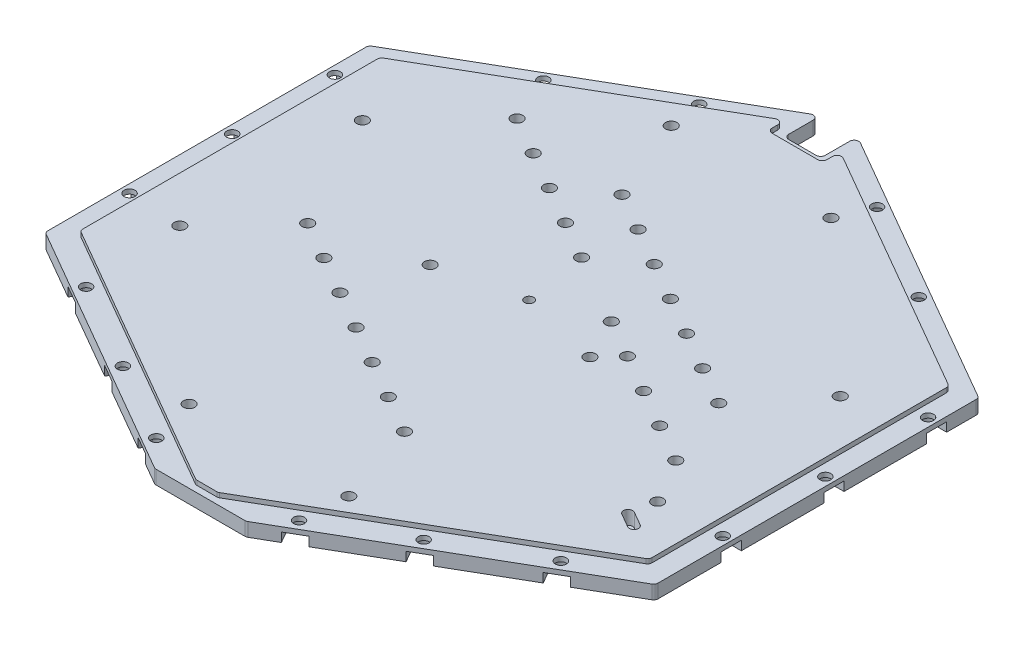
SolidWorks part; units mm, degrees
material "Copper"
ref_plane "Front Plane" through (0, 0, 0) normal (0, 0, 1) x (1, 0, 0)
ref_plane "Top Plane" through (0, 0, 0) normal (0, 1, 0) x (1, 0, 0)
ref_plane "Right Plane" through (0, 0, 0) normal (1, 0, 0) x (0, 0, -1)
sketch "Sketch1" plane through (0, 0, 0) normal (0, 1, 0) x (1, 0, 0)
  line L1 (-67.3538, -38.8868) -> (0, -77.7735)
  line L2 (0, -77.7735) -> (67.3538, -38.8868)
  line L3 (67.3538, -38.8868) -> (67.3538, 38.8868)
  line L4 (67.3538, 38.8868) -> (0, 77.7735)
  line L5 (0, 77.7735) -> (-67.3538, 38.8868)
  line L6 (-67.3538, 38.8868) -> (-67.3538, -38.8868)
  line L7 (-62.3538, -36) -> (0, -72) construction
  line L8 (0, -72) -> (62.3538, -36) construction
  line L9 (62.3538, -36) -> (62.3538, 36) construction
  line L10 (62.3538, 36) -> (0, 72) construction
  line L11 (0, 72) -> (-62.3538, 36) construction
  line L12 (-62.3538, 36) -> (-62.3538, -36) construction
  circle A0 centre (0, 0) radius 67.3538 construction
  circle A1 centre (0, 0) radius 62.3538 construction
  dimension "D1" = 5
  dimension "D2" = 72
extrude "Boss-Extrude1" add sketch "Sketch1" along normal blind 4
sketch "Sketch2" plane through (0, 4, 0) normal (0, 1, 0) x (1, 0, 0)
  line L0 (-67.3538, 38.8868) -> (-67.3538, 31.9585)
  line L1 (-67.3538, 38.8868) -> (-67.3538, -38.8868) construction
  line L2 (-67.3538, 31.9585) -> (0, 70.8453)
  line L3 (0, 70.8453) -> (67.3538, 31.9585)
  line L4 (67.3538, -38.8868) -> (67.3538, 38.8868) construction
  line L5 (67.3538, 31.9585) -> (67.3538, 38.8868)
  line L6 (67.3538, 38.8868) -> (0, 77.7735)
  line L7 (0, 77.7735) -> (-67.3538, 38.8868)
  line L8 (0, 77.7735) -> (-67.3538, 38.8868) construction
  dimension "D1" = 6
extrude "Cut-Extrude1" cut sketch "Sketch2" against normal up to next
sketch "Sketch4" plane through (0, 4, 0) normal (0, 1, 0) x (1, 0, 0)
  line L0 (-67.3538, 31.9585) -> (-67.3538, -38.8868)
  line L1 (-67.3538, 31.9585) -> (-67.3538, -38.8868) construction
  line L2 (-67.3538, -38.8868) -> (0, -77.7735)
  line L3 (0, -77.7735) -> (67.3538, -38.8868)
  line L4 (67.3538, -38.8868) -> (67.3538, 31.9585)
  line L7 (62.3538, 29.6491) -> (62.3538, -36)
  line L8 (62.3538, -36) -> (0, -72)
  line L9 (0, -72) -> (-62.3538, -36)
  line L10 (-62.3538, -36) -> (-62.3538, 29.6491)
  line L30 (-67.3538, 31.9585) -> (0, 70.8453)
  line L39 (0, 70.8453) -> (67.3538, 31.9585)
  line L40 (-62.3538, 29.6491) -> (0, 65.6491)
  line L41 (0, 65.6491) -> (62.3538, 29.6491)
  dimension "D1" = 5
  dimension "D2" = 5
  dimension "D3" = 5
  dimension "D4" = 4.5
extrude "Cut-Extrude3" cut sketch "Sketch4" against normal blind 1
sketch "Sketch5" plane through (0, 0, 0) normal (0, -1, 0) x (1, 0, 0)
  line L0 (0, 77.7735) -> (10, 72)
  line L1 (0, 77.7735) -> (67.3538, 38.8868) construction
  line L2 (10, 72) -> (-10, 72)
  line L3 (-67.3538, 38.8868) -> (0, 77.7735) construction
  line L4 (-10, 72) -> (0, 77.7735)
  line L5 (-4, -68.5359) -> (-4, -59.8859)
  line L6 (0, -70.8453) -> (0, -59.8859) construction
  line L7 (-4, -59.8859) -> (4, -59.8859)
  line L8 (4, -59.8859) -> (4, -68.5359)
  line L10 (4, -68.5359) -> (0, -70.8453)
  line L11 (0, -70.8453) -> (-4, -68.5359)
  line L15 (0, -70.8453) -> (-67.3538, -31.9585) construction
  line L16 (67.3538, -31.9585) -> (0, -70.8453) construction
  point P5 (0, 72)
  dimension "D1" = 8.65
  dimension "D2" = 8
extrude "Cut-Extrude4" cut sketch "Sketch5" against normal up to surface (3 mm away) up to face at (0, 3, 3.1754)
sketch "Sketch8" plane through (0, 4, 0) normal (0, 1, 0) x (1, 0, 0)
  line L0 (54.3431, -31.375) -> (51.312, -29.625) construction
  line L1 (53.8431, -32.241) -> (50.812, -30.491)
  line L2 (54.8431, -30.509) -> (51.812, -28.759)
  line L4 (-62.3538, 36) -> (62.3538, -36) construction
  line L7 (62.3538, 29.6491) -> (0, 65.6491) construction
  line L8 (0, 72) -> (0, -72) construction
  circle A0 centre (0, 0) radius 1
  arc A2 (53.8431, -32.241) -> (54.8431, -30.509) centre (54.3431, -31.375) ccw
  arc A3 (51.812, -28.759) -> (50.812, -30.491) centre (51.312, -29.625) ccw
  point P6 (52.8275, -30.5)
  dimension "D1" = 2
  dimension "D2" = 1
  dimension "D3" = 3.5
  dimension "D4" = 61
extrude "Cut-Extrude5" cut sketch "Sketch8" against normal offset from surface (3 mm away) 1 up to face at (0, 0, -9.8987)
sketch "Sketch16" plane through (0, 0, 0) normal (0, -1, 0) x (1, 0, 0)
  line L0 (67.3538, 38.8868) -> (66.8538, 39.1754)
  line L2 (-66.8538, -31.6699) -> (-66.8538, 39.1754)
  line L4 (67.3538, -31.9585) -> (67.3538, 38.8868)
  line L5 (67.3538, 38.8868) -> (67.3538, -38.8868) construction
  line L6 (0, 77.7735) -> (67.3538, 38.8868) construction
  line L7 (-67.3538, 38.8868) -> (-66.8538, 39.1754)
  line L9 (66.8538, -31.6699) -> (66.8538, 39.1754)
  line L11 (-67.3538, -31.9585) -> (-67.3538, 38.8868)
  line L12 (-67.3538, 38.8868) -> (0, 77.7735) construction
  line L13 (-67.3538, -38.8868) -> (-67.3538, 38.8868) construction
  line L15 (66.8538, -31.6699) -> (0, -70.2679)
  line L16 (0, -70.2679) -> (-66.8538, -31.6699)
  line L18 (-67.3538, -31.9585) -> (0, -70.8453)
  line L20 (0, -70.8453) -> (67.3538, -31.9585)
  line L22 (67.3538, -31.9585) -> (4, -68.5359) construction
  line L23 (-4, -68.5359) -> (-67.3538, -31.9585) construction
  line L24 (67.3538, 38.8868) -> (67.3538, -31.9585) construction
  dimension "D1" = 0.5
  dimension "D2" = 0.5
  dimension "D3" = 0.5
  dimension "D4" = 0.5
extrude "Cut-Extrude7" cut sketch "Sketch16" against normal through all
hole_wizard "Tap Drill for M3x0.5 Tap1" positions "Sketch9" profile "Sketch10" hole size "M3x0.5" standard "ANSI Metric" end condition through all
sketch "Sketch9" plane through (0, 4, 0) normal (0, 1, 0) x (1, 0, 0)
  line L0 (-5.9392, -68.571) -> (11.3328, -38.655) construction
  line L2 (-62.3538, -36) -> (0, -72) construction
  line L3 (-62.3538, -36) -> (0, -72) construction
  line L4 (-51.8644, 5.1642) -> (-35.7354, 33.1005) construction
  line L5 (-51.8644, 5.1642) -> (-18.4289, -14.1398) construction
  line L6 (-35.7354, 33.1005) -> (-2.2999, 13.7965) construction
  line L7 (-18.4289, -14.1398) -> (-2.2999, 13.7965) construction
  line L8 (-3.0309, -23.0298) -> (13.0981, 4.9065) construction
  line L9 (-3.0309, -23.0298) -> (30.4046, -42.3338) construction
  line L10 (13.0981, 4.9065) -> (46.5336, -14.3975) construction
  line L11 (30.4046, -42.3338) -> (46.5336, -14.3975) construction
  line L12 (-18.9587, 30.7468) -> (-16.9267, 34.2663) construction
  line L13 (-18.9587, 30.7468) -> (38.3216, -2.324) construction
  line L14 (-16.9267, 34.2663) -> (40.3536, 1.1956) construction
  line L15 (38.3216, -2.324) -> (40.3536, 1.1956) construction
  point P0 (11.3328, -38.655)
  point P1 (46.5336, -14.3975)
  point P3 (40.3536, 1.1956)
  point P411 (2.9739, -33.829)
  point P412 (-5.385, -29.003)
  point P413 (-13.7438, -24.177)
  point P414 (-22.1027, -19.351)
  point P415 (-30.4616, -14.525)
  point P416 (-38.8205, -9.699)
  point P431 (38.1747, -9.5715)
  point P432 (29.8158, -4.7455)
  point P433 (21.4569, 0.0805)
  point P434 (13.0981, 4.9065)
  point P437 (-2.2999, 13.7965)
  point P443 (-10.6588, 18.6225)
  point P444 (-19.0176, 23.4485)
  point P445 (-27.3765, 28.2745)
  point P446 (-35.7354, 33.1005)
  point P454 (31.9947, 6.0216)
  point P455 (23.6358, 10.8476)
  point P456 (15.2769, 15.6736)
  point P457 (6.9181, 20.4996)
  point P458 (-1.4408, 25.3256)
  point P459 (-9.7997, 30.1516)
  dimension "D1" = 34.544
  dimension "D2" = 6.858
  dimension "D3" = 7
  dimension "D4" = 32.258
  dimension "D5" = 4.064
  dimension "D6" = 32.258
  dimension "D7" = 6.35
  dimension "D8" = 6.35
  dimension "D11" = 4.826
  dimension "D12" = 7
  dimension "D13" = 8.89
  dimension "D14" = 8.89
  dimension "D9" = 5
  dimension "D10" = 5
sketch "Sketch10" plane through (11.3328, 4, 38.655) normal (1, 0, 0) x (0, 0, 1)
  line L0 (0, 0) -> (0, 4)
  line L1 (0, 4) -> (1.25, 4)
  line L2 (1.25, 4) -> (1.25, 0)
  line L5 (1.25, 0) -> (0, 0)
  line L11 (0, -6.35) -> (0, 107.95) construction
  dimension "Thru Hole Dia." = 2.5
  dimension "Thru Hole Depth" = 4
hole_wizard "Tap Drill for M3x0.5 Tap2" positions "Sketch11" profile "Sketch12" hole size "M3x0.5" standard "ANSI Metric" end condition through all
sketch "Sketch11" plane through (0, 0, 0) normal (0, -1, 0) x (-1, 0, 0)
  line L3 (17.5, -57) -> (-17.5, -57) construction
  line L4 (17.5, -57) -> (17.5, 48.637) construction
  line L5 (17.5, 48.637) -> (-17.5, 48.637) construction
  line L6 (-17.5, -57) -> (-17.5, 48.637) construction
  line L8 (52.3538, -24.1815) -> (-52.3538, -24.1815) construction
  line L9 (52.3538, -24.1815) -> (52.3538, 15.8185) construction
  line L10 (52.3538, 15.8185) -> (-52.3538, 15.8185) construction
  line L11 (-52.3538, -24.1815) -> (-52.3538, 15.8185) construction
  line L12 (-4, 59.8859) -> (4, 59.8859) construction
  line L15 (10, -72) -> (-10, -72) construction
  line L16 (0, -72) -> (0, 59.8859) construction
  line L17 (52.3538, -4.1815) -> (-52.3538, -4.1815) construction
  line L18 (-67.3538, -38.8868) -> (-67.3538, 38.8868) construction
  line L19 (67.3538, 38.8868) -> (67.3538, -38.8868) construction
  point P0 (-17.5, 48.637)
  point P2 (17.5, 48.637)
  point P8 (-52.3538, 15.8185)
  point P12 (-52.3538, -24.1815)
  point P20 (-17.5, -57)
  point P22 (17.5, -57)
  point P24 (52.3538, 15.8185)
  point P26 (52.3538, -24.1815)
  point P424 (0, 48.637)
  point P440 (17.5, -4.1815)
  point P441 (-17.5, -4.1815)
  dimension "D1" = 105.637
  dimension "D2" = 15
  dimension "D3" = 15
  dimension "D4" = 15
  dimension "D5" = 35
  dimension "D6" = 40
sketch "Sketch12" plane through (17.5, 0, -48.637) normal (1, 0, 0) x (0, 0, -1)
  line L0 (0, 0) -> (0, 4)
  line L1 (0, 4) -> (1.25, 4)
  line L2 (1.25, 4) -> (1.25, 0)
  line L5 (1.25, 0) -> (0, 0)
  line L11 (0, -6.35) -> (0, 107.95) construction
  dimension "Thru Hole Dia." = 2.5
  dimension "Thru Hole Depth" = 4
chamfer "Chamfer1" distance 2.8 1 edges at (0, 3.5, 72)
hole_wizard "CBORE for M2 SHCS2" positions "Sketch13" profile "Sketch14" counterbore size "M2" standard "ANSI Metric" end condition through all
sketch "Sketch13" plane through (0, 0, 79.328) normal (0, -1, 0) x (-1, 0, 0)
  point P0 (-65, 101.7487)
  point P1 (-41.1362, 123.5785)
  point P2 (-19.4856, 136.0785)
  point P3 (19.4856, 136.0785)
  point P4 (41.1362, 123.5785)
  point P5 (65, 101.7687)
  point P6 (65, 79.2687)
  point P7 (65, 56.7687)
  point P8 (52.0096, 34.2687)
  point P9 (32.9571, 23.2687)
  point P10 (15.6366, 13.2687)
  point P11 (-15.6366, 13.2687)
  point P12 (-32.9571, 23.2687)
  point P13 (-52.0096, 34.2687)
  point P14 (-65, 56.7487)
  point P15 (-65, 79.2487)
sketch "Sketch14" plane through (65, 0, -22.4207) normal (1, 0, 0) x (0, 0, -1)
  line L0 (0, 0) -> (0, 4)
  line L1 (0, 4) -> (1.2, 4)
  line L2 (1.2, 4) -> (1.2, 2)
  line L3 (1.2, 2) -> (2.2, 2)
  line L4 (2.2, 2) -> (2.2, 0)
  line L5 (2.2, 0) -> (0, 0)
  line L6 (0, -6.35) -> (0, 107.95) construction
  dimension "Thru Hole Dia." = 2.4
  dimension "Thru Hole Depth" = 4
  dimension "C'Bore Dia." = 4.4
  dimension "C'Bore Depth" = 2
sketch "Sketch15" plane through (0, 4, 0) normal (0, 1, 0) x (1, 0, 0)
  line L1 (6, 73.0491) -> (-6, 73.0491)
  line L2 (6, 73.0491) -> (6, 58.2491)
  line L3 (6, 58.2491) -> (-6, 58.2491)
  line L4 (-6, 73.0491) -> (-6, 58.2491)
  line L5 (6, 73.0491) -> (-6, 58.2491) construction
  line L6 (6, 58.2491) -> (-6, 73.0491) construction
  point P0 (0, 65.6491)
  dimension "D1" = 12
  dimension "D2" = 7.4
extrude "Cut-Extrude6" cut sketch "Sketch15" against normal up to surface (1 mm away) up to face at (65, 3, -23.6207)
fillet "Fillet1" radius 1 20 edges at (4, 1.5, -59.8859) (-4, 1.5, -59.8859) (62.3538, 3.5, -29.6491) (62.3538, 3.5, 36) (10, 1.5, 72) (-10, 1.5, 72) (-62.3538, 3.5, 36) (-62.3538, 3.5, -29.6491) (66.8538, 1.5, 39.1754) (66.8538, 1.5, -31.6699) (-66.8538, 1.5, 39.1754) (-66.8538, 1.5, -31.6699) (4, 1.5, -67.9585) (-4, 1.5, -67.9585) (6, 3.5, -58.2491) (-6, 3.5, -58.2491) (6, 3.5, -62.185) (-6, 3.5, -62.185) (-2.4249, 3.5, 70.6) (2.4249, 3.5, 70.6)
sketch "Sketch17" plane through (0, 0, 0) normal (0, -1, 0) x (1, 0, 0)
  line L0 (-65, 24.7593) -> (-66.8538, 24.7593)
  line L1 (21.3908, -55.6505) -> (22.3726, -57.3511)
  line L2 (-65, 20.3593) -> (-66.8538, 20.3593)
  line L3 (22.3726, -57.3511) -> (18.5621, -59.5511)
  line L4 (-66.8538, 20.3593) -> (-66.8538, 24.7593)
  line L5 (18.5621, -59.5511) -> (17.5803, -57.8505)
  line L6 (21.3908, -55.6505) -> (17.5803, -57.8505) construction
  line L7 (-65, 2.2593) -> (-66.8538, 2.2593)
  line L8 (-65, -2.1407) -> (-66.8538, -2.1407)
  line L9 (-66.8538, -2.1407) -> (-66.8538, 2.2593)
  line L10 (-65, -20.2407) -> (-66.8538, -20.2407)
  line L11 (-65, -24.6407) -> (-66.8538, -24.6407)
  line L12 (-66.8538, -24.6407) -> (-66.8538, -20.2407)
  line L13 (0, -2.2) -> (0, 2.2) construction
  line L14 (66.8538, -24.6407) -> (66.8538, -20.2407)
  line L15 (65, -24.6407) -> (66.8538, -24.6407)
  line L16 (65, -20.2407) -> (66.8538, -20.2407)
  line L17 (66.8538, -2.1407) -> (66.8538, 2.2593)
  line L18 (65, -2.1407) -> (66.8538, -2.1407)
  line L19 (65, 2.2593) -> (66.8538, 2.2593)
  line L20 (66.8538, 20.3593) -> (66.8538, 24.7593)
  line L21 (65, 20.3593) -> (66.8538, 20.3593)
  line L22 (65, 24.7593) -> (66.8538, 24.7593)
  line L23 (53.9149, 43.9593) -> (50.1044, 46.1593) construction
  line L24 (10.2321, 71.866) -> (66.3538, 39.4641) construction
  line L25 (-66.8538, 23.7439) -> (-66.8538, 38.5981) construction
  line L26 (-66.8538, 1.2439) -> (-66.8538, 21.3747) construction
  line L27 (43.0415, -43.1505) -> (39.231, -45.3505) construction
  line L28 (66.3538, -31.9585) -> (42.9772, -45.4551) construction
  line L29 (43.0415, -43.1505) -> (44.0233, -44.8511)
  line L30 (44.0233, -44.8511) -> (40.2128, -47.0511)
  line L31 (41.2589, -46.4471) -> (21.3265, -57.9551) construction
  line L32 (40.2128, -47.0511) -> (39.231, -45.3505)
  line L33 (53.9149, 43.9593) -> (55.0781, 45.9741)
  line L34 (55.0781, 45.9741) -> (51.2676, 48.1741)
  line L35 (51.2676, 48.1741) -> (50.1044, 46.1593)
  line L36 (34.8623, 54.9593) -> (36.0256, 56.9741)
  line L37 (36.0256, 56.9741) -> (32.2151, 59.1741)
  line L38 (32.2151, 59.1741) -> (31.0518, 57.1593)
  line L39 (34.8623, 54.9593) -> (31.0518, 57.1593) construction
  line L40 (17.5418, 64.9593) -> (18.7051, 66.9741)
  line L41 (18.7051, 66.9741) -> (14.8946, 69.1741)
  line L42 (14.8946, 69.1741) -> (13.7313, 67.1593)
  line L43 (17.5418, 64.9593) -> (13.7313, 67.1593) construction
  line L44 (-17.5418, 64.9593) -> (-13.7313, 67.1593) construction
  line L45 (-34.8623, 54.9593) -> (-31.0518, 57.1593) construction
  line L46 (-43.0415, -43.1505) -> (-39.231, -45.3505) construction
  line L47 (-53.9149, 43.9593) -> (-50.1044, 46.1593) construction
  line L48 (-21.3908, -55.6505) -> (-17.5803, -57.8505) construction
  line L49 (-14.8946, 69.1741) -> (-13.7313, 67.1593)
  line L50 (-18.7051, 66.9741) -> (-14.8946, 69.1741)
  line L51 (-17.5418, 64.9593) -> (-18.7051, 66.9741)
  line L52 (-32.2151, 59.1741) -> (-31.0518, 57.1593)
  line L53 (-36.0256, 56.9741) -> (-32.2151, 59.1741)
  line L54 (-34.8623, 54.9593) -> (-36.0256, 56.9741)
  line L55 (-51.2676, 48.1741) -> (-50.1044, 46.1593)
  line L56 (-55.0781, 45.9741) -> (-51.2676, 48.1741)
  line L57 (-53.9149, 43.9593) -> (-55.0781, 45.9741)
  line L58 (-40.2128, -47.0511) -> (-39.231, -45.3505)
  line L59 (-44.0233, -44.8511) -> (-40.2128, -47.0511)
  line L60 (-43.0415, -43.1505) -> (-44.0233, -44.8511)
  line L61 (-18.5621, -59.5511) -> (-17.5803, -57.8505)
  line L62 (-22.3726, -57.3511) -> (-18.5621, -59.5511)
  line L63 (-21.3908, -55.6505) -> (-22.3726, -57.3511)
  arc A0 (-65, 20.3593) -> (-65, 24.7593) centre (-65, 22.5593) ccw
  arc A1 (-66.8538, 21.3747) -> (-66.8538, 23.7439) centre (-65, 22.5593) ccw construction
  arc A2 (-66.8538, 21.3747) -> (-66.8538, 23.7439) centre (-65, 22.5593) ccw construction
  arc A3 (-65, -2.1407) -> (-65, 2.2593) centre (-65, 0.0593) ccw
  arc A4 (-65, -24.6407) -> (-65, -20.2407) centre (-65, -22.4407) ccw
  arc A5 (65, -24.6407) -> (65, -20.2407) centre (65, -22.4407) cw
  arc A6 (65, -2.1407) -> (65, 2.2593) centre (65, 0.0593) cw
  arc A7 (65, 20.3593) -> (65, 24.7593) centre (65, 22.5593) cw
  arc A8 (39.231, -45.3505) -> (43.0415, -43.1505) centre (41.1362, -44.2505) cw
  arc A9 (42.9772, -45.4551) -> (41.2589, -46.4471) centre (41.1362, -44.2505) ccw construction
  arc A10 (17.5803, -57.8505) -> (21.3908, -55.6505) centre (19.4856, -56.7505) cw
  arc A11 (53.9149, 43.9593) -> (50.1044, 46.1593) centre (52.0096, 45.0593) cw
  circle A12 centre (52.0096, 45.0593) radius 2.2 construction
  arc A13 (34.8623, 54.9593) -> (31.0518, 57.1593) centre (32.9571, 56.0593) cw
  arc A14 (17.5418, 64.9593) -> (13.7313, 67.1593) centre (15.6366, 66.0593) cw
  arc A15 (-17.5418, 64.9593) -> (-13.7313, 67.1593) centre (-15.6366, 66.0593) ccw
  arc A16 (-34.8623, 54.9593) -> (-31.0518, 57.1593) centre (-32.9571, 56.0593) ccw
  arc A17 (-53.9149, 43.9593) -> (-50.1044, 46.1593) centre (-52.0096, 45.0593) ccw
  arc A18 (-17.5803, -57.8505) -> (-21.3908, -55.6505) centre (-19.4856, -56.7505) ccw
  arc A19 (-39.231, -45.3505) -> (-43.0415, -43.1505) centre (-41.1362, -44.2505) ccw
  dimension "D1" = 3
  dimension "D2" = 2
  dimension "D3" = 2
  dimension "D4" = 2
extrude "Cut-Extrude8" cut sketch "Sketch17" against normal up to surface (2 mm away) up to face at (-65, 2, -1.1407)
